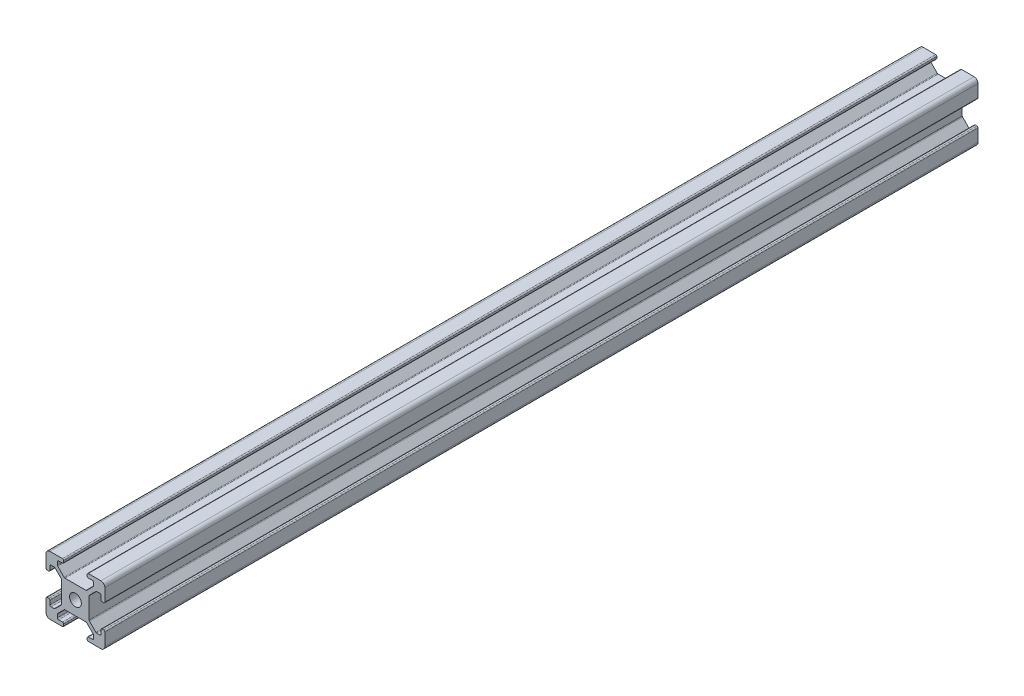
SolidWorks part; units mm, degrees
ref_plane "Front Plane" through (0, 0, 0) normal (0, 0, 1) x (1, 0, 0)
ref_plane "Top Plane" through (0, 0, 0) normal (0, 1, 0) x (1, 0, 0)
ref_plane "Right Plane" through (0, 0, 0) normal (1, 0, 0) x (0, 0, -1)
sketch "Sketch1" plane through (0, 0, 0) normal (0, 0, 1) x (1, 0, 0)
  line L0 (0.9971, -0.011) -> (4.1971, -0.011)
  line L1 (14.9971, 0.989) -> (14.9971, 4.189)
  line L2 (13.9971, 14.989) -> (10.7971, 14.989)
  line L3 (-0.0029, 13.989) -> (-0.0029, 10.789)
  line L4 (4.4971, 0.289) -> (4.4971, 0.689)
  line L5 (10.4971, 0.289) -> (10.4971, 0.689)
  line L6 (4.4971, 14.689) -> (4.4971, 14.289)
  line L7 (10.4971, 14.689) -> (10.4971, 14.289)
  line L8 (4.1971, 14.989) -> (0.9971, 14.989)
  line L9 (10.7971, -0.011) -> (13.9971, -0.011)
  line L10 (0.9971, 4.189) -> (0.9971, 3.189)
  line L11 (0.9971, 10.789) -> (0.9971, 11.7902)
  line L12 (14.6971, 10.5) -> (14.3, 10.5)
  line L13 (14.6971, 4.489) -> (14.3053, 4.489)
  line L14 (0.2971, 4.489) -> (0.6971, 4.489)
  line L15 (0.2971, 10.489) -> (0.6971, 10.489)
  line L16 (-0.0029, 4.189) -> (-0.0029, 0.989)
  line L17 (14.9971, 10.8) -> (14.9971, 13.989)
  line L18 (14, 10.8) -> (14, 11.8)
  line L19 (14.0053, 4.189) -> (14.0053, 3.189)
  line L20 (4.8302, 10.985) -> (10.1675, 10.985)
  line L21 (10.9699, 10.1634) -> (10.9699, 4.8261)
  line L22 (10.1715, 3.9947) -> (4.8343, 3.9947)
  line L23 (4.0029, 4.8261) -> (4.0029, 10.1634)
  line L24 (4.1971, 13.989) -> (3.1971, 13.989)
  line L25 (10.7971, 13.989) -> (11.7988, 13.989)
  line L26 (4.1971, 0.989) -> (3.1971, 0.989)
  line L27 (10.7971, 0.989) -> (11.8086, 0.989)
  line L28 (1.2971, 12.0902) -> (2.0579, 12.0902)
  line L29 (2.8971, 13.689) -> (2.8971, 12.9204)
  line L30 (1.2971, 2.889) -> (2.0658, 2.889)
  line L31 (2.8971, 1.289) -> (2.8971, 2.0576)
  line L32 (4.6181, 11.0728) -> (2.9867, 12.7042)
  line L33 (3.9121, 10.3808) -> (2.2729, 12.0018)
  line L34 (10.3796, 11.0728) -> (12.011, 12.7042)
  line L35 (11.0879, 10.3808) -> (12.7192, 12.0121)
  line L36 (11.0891, 4.6099) -> (12.7204, 2.9786)
  line L37 (10.3877, 3.9052) -> (12.0191, 2.2738)
  line L38 (4.6181, 3.9052) -> (2.9867, 2.2738)
  line L39 (3.9133, 4.6099) -> (2.282, 2.9786)
  line L40 (12.0988, 13.689) -> (12.0988, 12.9163)
  line L41 (13.7, 12.1) -> (12.9314, 12.1)
  line L42 (13.7053, 2.889) -> (12.9366, 2.889)
  line L43 (12.1086, 1.289) -> (12.1086, 2.0576)
  circle A0 centre (7.5, 7.5) radius 1.5
  arc A1 (0.9971, -0.011) -> (-0.0029, 0.989) centre (0.9971, 0.989) cw
  arc A2 (13.9971, -0.011) -> (14.9971, 0.989) centre (13.9971, 0.989) ccw
  arc A3 (14.9971, 13.989) -> (13.9971, 14.989) centre (13.9971, 13.989) ccw
  arc A4 (0.9971, 14.989) -> (-0.0029, 13.989) centre (0.9971, 13.989) ccw
  arc A5 (10.4971, 0.289) -> (10.7971, -0.011) centre (10.7971, 0.289) ccw
  arc A6 (10.4971, 0.689) -> (10.7971, 0.989) centre (10.7971, 0.689) cw
  arc A7 (4.4971, 0.289) -> (4.1971, -0.011) centre (4.1971, 0.289) cw
  arc A8 (4.4971, 0.689) -> (4.1971, 0.989) centre (4.1971, 0.689) ccw
  arc A9 (0.6971, 4.489) -> (0.9971, 4.189) centre (0.6971, 4.189) cw
  arc A10 (0.2971, 4.489) -> (-0.0029, 4.189) centre (0.2971, 4.189) ccw
  arc A11 (0.6971, 10.489) -> (0.9971, 10.789) centre (0.6971, 10.789) ccw
  arc A12 (0.2971, 10.489) -> (-0.0029, 10.789) centre (0.2971, 10.789) cw
  arc A13 (4.4971, 14.289) -> (4.1971, 13.989) centre (4.1971, 14.289) cw
  arc A14 (4.1971, 14.989) -> (4.4971, 14.689) centre (4.1971, 14.689) cw
  arc A15 (10.4971, 14.289) -> (10.7971, 13.989) centre (10.7971, 14.289) ccw
  arc A16 (10.7971, 14.989) -> (10.4971, 14.689) centre (10.7971, 14.689) ccw
  arc A17 (14.3053, 4.489) -> (14.0053, 4.189) centre (14.3053, 4.189) ccw
  arc A18 (14.9971, 4.189) -> (14.6971, 4.489) centre (14.6971, 4.189) ccw
  arc A19 (14.3, 10.5) -> (14, 10.8) centre (14.3, 10.8) cw
  arc A20 (14.9971, 10.8) -> (14.6971, 10.5) centre (14.6971, 10.8) cw
  arc A21 (11.7988, 13.989) -> (12.0988, 13.689) centre (11.7988, 13.689) cw
  arc A22 (14, 11.8) -> (13.7, 12.1) centre (13.7, 11.8) ccw
  arc A23 (14.0053, 3.189) -> (13.7053, 2.889) centre (13.7053, 3.189) cw
  arc A24 (11.8086, 0.989) -> (12.1086, 1.289) centre (11.8086, 1.289) ccw
  arc A25 (3.1971, 0.989) -> (2.8971, 1.289) centre (3.1971, 1.289) cw
  arc A26 (0.9971, 3.189) -> (1.2971, 2.889) centre (1.2971, 3.189) ccw
  arc A27 (0.9971, 11.7902) -> (1.2971, 12.0902) centre (1.2971, 11.7902) cw
  arc A28 (3.1971, 13.989) -> (2.8971, 13.689) centre (3.1971, 13.689) ccw
  arc A29 (10.3796, 11.0728) -> (10.1675, 10.985) centre (10.1675, 11.285) cw
  arc A30 (12.0988, 12.9163) -> (12.011, 12.7042) centre (11.7988, 12.9163) cw
  arc A31 (4.6181, 11.0728) -> (4.8302, 10.985) centre (4.8302, 11.285) ccw
  arc A32 (12.9314, 12.1) -> (12.7192, 12.0121) centre (12.9314, 11.8) ccw
  arc A33 (10.9699, 10.1634) -> (11.0879, 10.3808) centre (11.2692, 10.1417) cw
  arc A34 (11.0891, 4.6099) -> (10.9699, 4.8261) centre (11.269, 4.85) cw
  arc A35 (12.9366, 2.889) -> (12.7204, 2.9786) centre (12.9366, 3.1947) cw
  arc A36 (12.1086, 2.0576) -> (12.0191, 2.2738) centre (11.8029, 2.0576) ccw
  arc A37 (2.8971, 2.0576) -> (2.9867, 2.2738) centre (3.2029, 2.0576) cw
  arc A38 (10.3877, 3.9052) -> (10.1715, 3.9947) centre (10.1715, 3.689) ccw
  arc A39 (4.6181, 3.9052) -> (4.8343, 3.9947) centre (4.8343, 3.689) cw
  arc A40 (2.0658, 2.889) -> (2.282, 2.9786) centre (2.0658, 3.1947) ccw
  arc A41 (3.9133, 4.6099) -> (4.0029, 4.8261) centre (3.6971, 4.8261) ccw
  arc A42 (3.9121, 10.3808) -> (4.0029, 10.1634) centre (3.6971, 10.1634) cw
  arc A43 (2.8971, 12.9204) -> (2.9867, 12.7042) centre (3.2029, 12.9204) ccw
  arc A44 (2.0579, 12.0902) -> (2.2729, 12.0018) centre (2.0579, 11.7845) cw
extrude "Boss-Extrude1" add sketch "Sketch1" along normal blind 222.5
